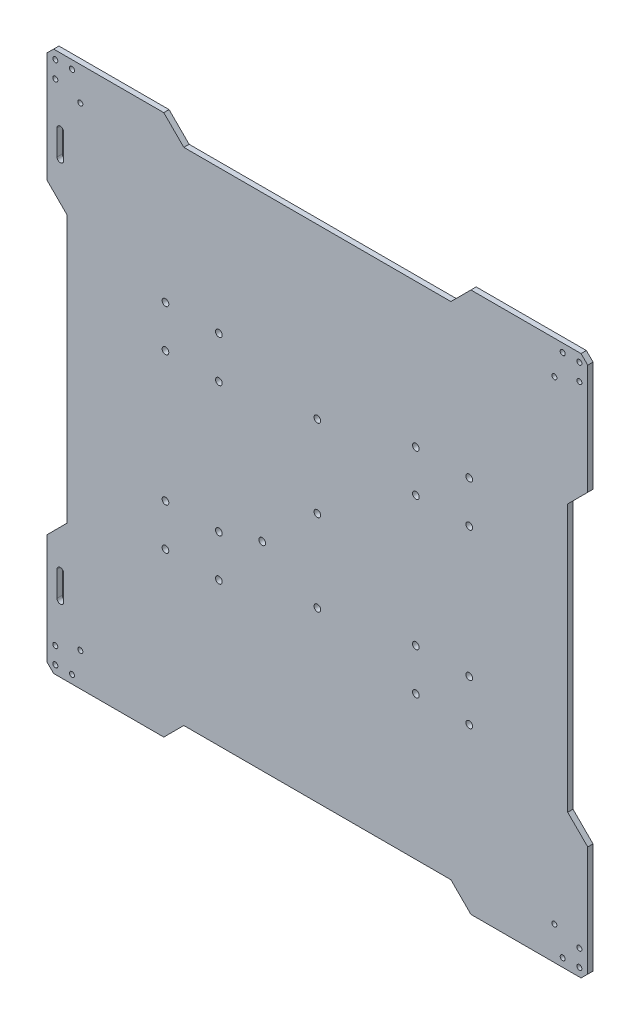
SolidWorks part; units mm, degrees
material "7050-T7651"
ref_plane "Front Plane" through (0, 0, 0) normal (0, 0, 1) x (1, 0, 0)
ref_plane "Top Plane" through (0, 0, 0) normal (0, 1, 0) x (1, 0, 0)
ref_plane "Right Plane" through (0, 0, 0) normal (1, 0, 0) x (0, 0, -1)
sketch "Sketch1" plane through (0, 0, 0) normal (0, 0, 1) x (1, 0, 0)
  line L0 (-157, 157) -> (157, -157) construction
  line L1 (-59, -39) -> (59, 39) construction
  line L2 (-91, 67.5) -> (-59, 67.5) construction
  line L3 (-91, 67.5) -> (-91, 39) construction
  line L4 (-91, 39) -> (-59, 39) construction
  line L5 (-59, 67.5) -> (-59, 39) construction
  line L6 (-91, -39) -> (-59, -39) construction
  line L7 (-91, -39) -> (-91, -67.5) construction
  line L8 (-91, -67.5) -> (-59, -67.5) construction
  line L9 (-59, -39) -> (-59, -67.5) construction
  line L10 (59, -39) -> (91, -39) construction
  line L11 (59, -39) -> (59, -67.5) construction
  line L12 (59, -67.5) -> (91, -67.5) construction
  line L13 (91, -39) -> (91, -67.5) construction
  line L14 (59, 67.5) -> (91, 67.5) construction
  line L15 (59, 67.5) -> (59, 39) construction
  line L16 (59, 39) -> (91, 39) construction
  line L17 (91, 67.5) -> (91, 39) construction
  line L18 (-75, 67.5) -> (-75, 39) construction
  line L19 (-75, -39) -> (-75, -67.5) construction
  line L20 (75, -39) -> (75, -67.5) construction
  line L21 (75, 39) -> (75, 67.5) construction
  line L22 (162, 162) -> (162, 92)
  line L23 (162, 92) -> (150, 80)
  line L24 (150, 80) -> (150, -80)
  line L25 (150, -80) -> (162, -92)
  line L26 (162, -92) -> (162, -162)
  line L27 (162, -162) -> (92, -162)
  line L28 (92, -162) -> (80, -150)
  line L29 (80, -150) -> (-80, -150)
  line L30 (-80, -150) -> (-92, -162)
  line L31 (-92, -162) -> (-162, -162)
  line L32 (-162, -162) -> (-162, -92)
  line L33 (-162, -92) -> (-150, -80)
  line L34 (-150, -80) -> (-150, 80)
  line L35 (-150, 80) -> (-162, 92)
  line L36 (-162, 92) -> (-162, 162)
  line L37 (-162, 162) -> (-92, 162)
  line L38 (-92, 162) -> (-80, 150)
  line L39 (-80, 150) -> (80, 150)
  line L40 (80, 150) -> (92, 162)
  line L41 (92, 162) -> (162, 162)
  line L42 (-27.2213, -27) -> (-12, -27) construction
  line L47 (-7, 32.8786) -> (-7, -22) construction
  line L48 (7, -32.8786) -> (7, 32.8786) construction
  line L49 (0, 49) -> (0, -49) construction
  circle A0 centre (-157, 157) radius 1.5
  circle A1 centre (157, 157) radius 1.5
  circle A2 centre (157, -157) radius 1.5
  circle A3 centre (-157, -157) radius 1.5
  arc A4 (-13.7143, 37.5755) -> (-31.1101, -25.1429) centre (0, 0) ccw construction
  circle A5 centre (-91, 64) radius 2
  circle A6 centre (-91, 39) radius 2
  circle A7 centre (-59, 39) radius 2
  circle A8 centre (-59, 64) radius 2
  circle A9 centre (59, 39) radius 2
  circle A10 centre (59, 64) radius 2
  circle A11 centre (91, 39) radius 2
  circle A12 centre (91, 64) radius 2
  circle A13 centre (59, -64) radius 2
  circle A14 centre (59, -39) radius 2
  circle A15 centre (91, -39) radius 2
  circle A16 centre (91, -64) radius 2
  circle A17 centre (-91, -64) radius 2
  circle A18 centre (-59, -64) radius 2
  circle A19 centre (-59, -39) radius 2
  circle A20 centre (-91, -39) radius 2
  circle A21 centre (-33, -31) radius 2
  arc A22 (13.7143, -37.5755) -> (13.7143, 37.5755) centre (0, 0) ccw construction
  arc A23 (-7, 32.8786) -> (-13.7143, 37.5755) centre (-12, 32.8786) ccw construction
  arc A24 (13.7143, 37.5755) -> (7, 32.8786) centre (12, 32.8786) ccw construction
  arc A25 (7, -32.8786) -> (13.7143, -37.5755) centre (12, -32.8786) ccw construction
  arc A26 (-31.1101, -25.1429) -> (-27.2213, -27) centre (-27.2213, -22) ccw construction
  circle A27 centre (0, 0) radius 2
  circle A28 centre (0, 49) radius 2
  circle A29 centre (0, -49) radius 2
  arc A30 (-7, -22) -> (-12, -27) centre (-12, -22) cw construction
  circle A31 centre (-147, 157) radius 1.5
  circle A32 centre (-157, 147) radius 1.5
  circle A33 centre (147, 157) radius 1.5
  circle A34 centre (157, 147) radius 1.5
  circle A35 centre (157, -147) radius 1.5
  circle A36 centre (147, -157) radius 1.5
  circle A37 centre (-147, -157) radius 1.5
  circle A38 centre (-157, -147) radius 1.5
  circle A39 centre (-142, 142) radius 1.5
  circle A40 centre (142, 142) radius 1.5
  circle A41 centre (142, -142) radius 1.5
  circle A42 centre (-142, -142) radius 1.5
  point P97 (7, -39.3827)
  dimension "D3" = 3
  dimension "D4" = 80
  dimension "D11" = 4
  dimension "D21" = 5
  dimension "D26" = 5
  dimension "D24" = 49
  dimension "D23" = 5
  dimension "D31" = 10
  dimension "D1" = 314
  dimension "D2" = 314
  dimension "D5" = 135
  dimension "D6" = 150
  dimension "D7" = 32
  dimension "D8" = 28.5
  dimension "D9" = 3.5
  dimension "D10" = 3.5
  dimension "D12" = 5
  dimension "D13" = 5
  dimension "D14" = 5
  dimension "D15" = 5
  dimension "D16" = 12
  dimension "D17" = 70
  dimension "D18" = 33
  dimension "D19" = 18
  dimension "D22" = 27
  dimension "D25" = 7
  dimension "D20" = 14
  dimension "D27" = 7
  dimension "D28" = 49
  dimension "D29" = 10
  dimension "D30" = 10
  dimension "D32" = 10
  dimension "D33" = 15
  dimension "D34" = 15
extrude "Boss-Extrude1" add sketch "Sketch1" along normal blind 3.175
sketch "Sketch2" plane through (0, 0, 3.175) normal (0, 0, 1) x (1, 0, 0)
  line L0 (-156, 122) -> (-156, 107)
  line L1 (-152, 107) -> (-152, 122)
  line L2 (-92, 162) -> (-162, 162) construction
  line L3 (-162, 162) -> (-162, 92) construction
  line L4 (-152, -107) -> (-152, -122)
  line L5 (-156, -122) -> (-156, -107)
  line L6 (-162, -162) -> (-92, -162) construction
  arc A0 (-152, 122) -> (-156, 122) centre (-154, 122) ccw
  arc A1 (-156, 107) -> (-152, 107) centre (-154, 107) ccw
  arc A2 (-152, -107) -> (-156, -107) centre (-154, -107) ccw
  arc A3 (-156, -122) -> (-152, -122) centre (-154, -122) ccw
  dimension "D1" = 4
  dimension "D2" = 40
  dimension "D3" = 15
  dimension "D4" = 8
  dimension "D5" = 40
extrude "Cut-Extrude1" cut sketch "Sketch2" against normal through all
chamfer "Chamfer1" distance 4 angle 45 4 edges at (-162, -162, 1.5875) (162, -162, 1.5875) (162, 162, 1.5875) (-162, 162, 1.5875)
